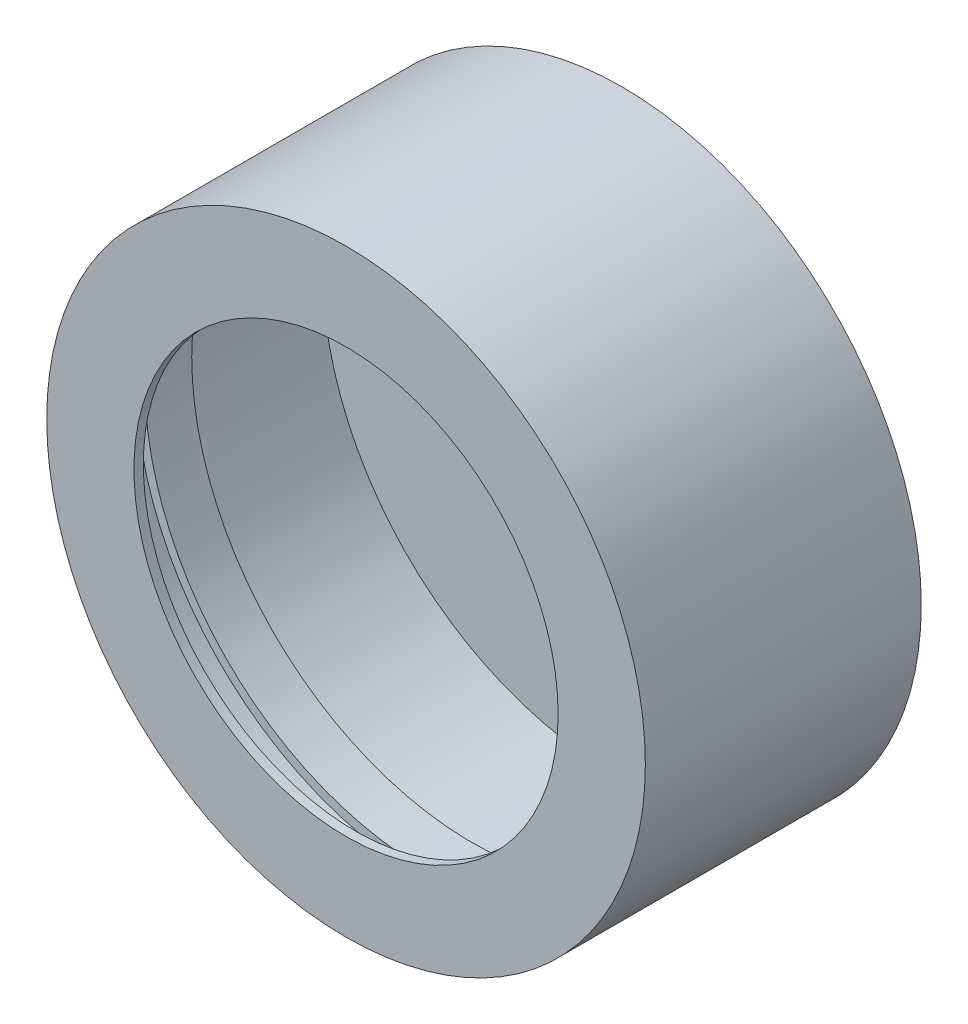
SolidWorks part; units mm, degrees
ref_plane "Front Plane" through (0, 0, 0) normal (0, 0, 1) x (1, 0, 0)
ref_plane "Top Plane" through (0, 0, 0) normal (0, 1, 0) x (1, 0, 0)
ref_plane "Right Plane" through (0, 0, 0) normal (1, 0, 0) x (0, 0, -1)
sketch "Sketch1" plane through (0, 0, 0) normal (0, 0, 1) x (1, 0, 0)
  circle A1 centre (0, 0) radius 64
  circle A2 centre (0, 0) radius 62
  circle A3 centre (0, 0) radius 62
  dimension "D1" = 0
  dimension "D2" = 2
extrude "Boss-Extrude1" add sketch "Sketch1" against normal blind 55
sketch "Sketch2" plane through (0, 0, -15) normal (0, 0, -1) x (-1, 0, 0)
  circle A1 centre (0, 0) radius 60
  circle A2 centre (0, 0) radius 62
  circle A3 centre (0, 0) radius 62
  dimension "D1" = 0
  dimension "D2" = 2
extrude "Boss-Extrude2" add sketch "Sketch2" along normal blind 10
sketch "Sketch3" plane through (0, 0, 0) normal (0, 0, 1) x (1, 0, 0)
  circle A2 centre (0, 0) radius 64
  circle A3 centre (0, 0) radius 64
  circle A5 centre (0, 0) radius 45.35
  circle A6 centre (0, 0) radius 45.35
  dimension "D1" = 0
  dimension "D2" = 0
extrude "Boss-Extrude3" add sketch "Sketch3" along normal blind 2
sketch "Sketch4" plane through (0, 0, -55) normal (0, 0, -1) x (-1, 0, 0)
  circle A2 centre (0, 0) radius 29
  circle A3 centre (0, 0) radius 29
  circle A5 centre (0, 0) radius 64
  circle A6 centre (0, 0) radius 64
  dimension "D1" = 0
  dimension "D2" = 0
extrude "Boss-Extrude4" add sketch "Sketch4" along normal blind 2
